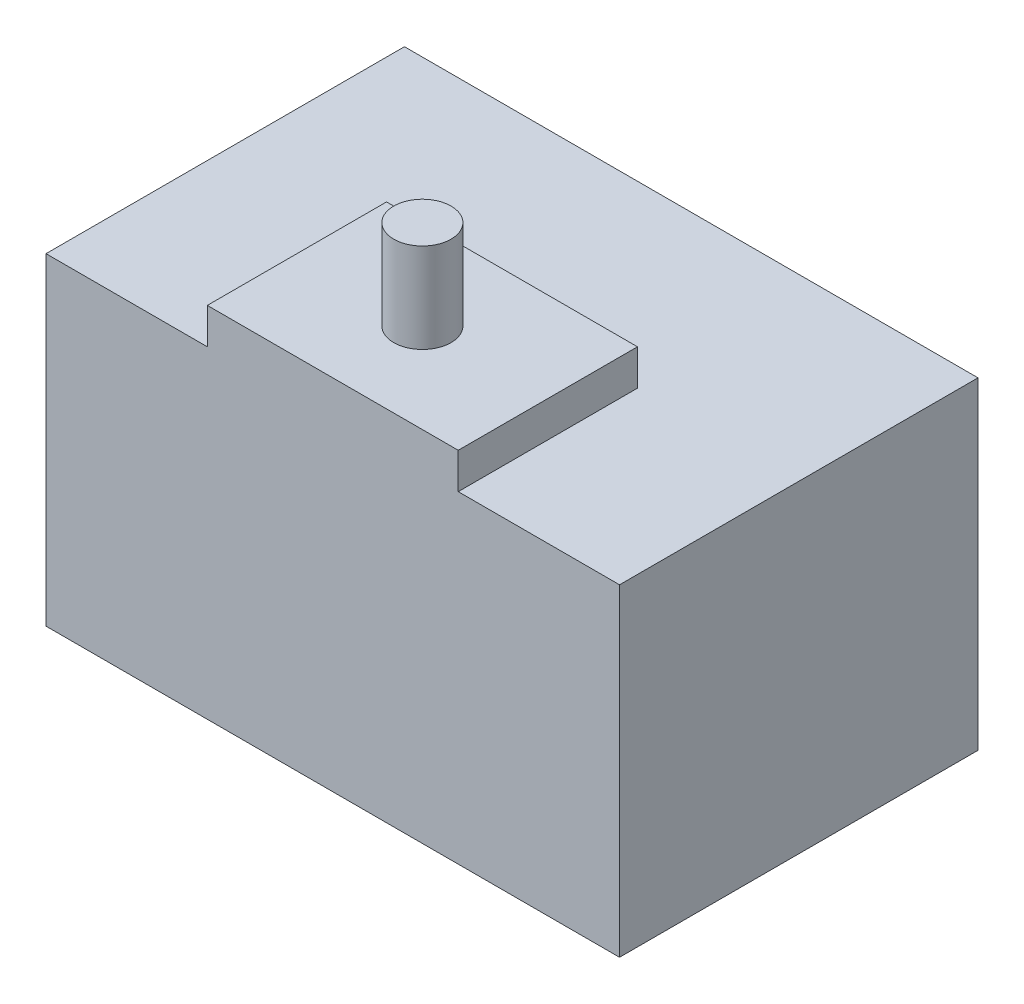
SolidWorks part; units mm, degrees
ref_plane "前视基准面" through (0, 0, 0) normal (0, 0, 1) x (1, 0, 0)
ref_plane "上视基准面" through (0, 0, 0) normal (0, 1, 0) x (1, 0, 0)
ref_plane "右视基准面" through (0, 0, 0) normal (1, 0, 0) x (0, 0, -1)
sketch "草图1" plane through (0, 0, 0) normal (0, 1, 0) x (1, 0, 0)
  line L1 (-800, 500) -> (800, 500)
  line L2 (-800, 500) -> (-800, -500)
  line L3 (-800, -500) -> (800, -500)
  line L4 (800, 500) -> (800, -500)
  line L5 (-800, 500) -> (800, -500) construction
  line L6 (-800, -500) -> (800, 500) construction
  point P0 (0, 0)
  dimension "D1" = 1600
  dimension "D2" = 1000
extrude "凸台-拉伸1" add sketch "草图1" along normal blind 900
sketch "草图2" plane through (0, 900, 0) normal (0, 1, 0) x (1, 0, 0)
  line L0 (-800, -500) -> (800, -500) construction
  line L1 (-350, 0) -> (350, 0)
  line L2 (-350, 0) -> (-350, -500)
  line L3 (-350, -500) -> (350, -500)
  line L4 (350, 0) -> (350, -500)
  line L5 (-350, 0) -> (350, -500) construction
  line L6 (-350, -500) -> (350, 0) construction
  point P0 (0, -250)
  dimension "D1" = 0
  dimension "D2" = 700
  dimension "D3" = 500
extrude "凸台-拉伸2" add sketch "草图2" along normal blind 100
sketch "草图3" plane through (0, 1000, 0) normal (0, 1, 0) x (1, 0, 0)
  line L0 (-350, 0) -> (-350, -500) construction
  line L1 (-300, -50) -> (300, -50) construction
  line L2 (-300, -50) -> (-300, -450) construction
  line L3 (-300, -450) -> (300, -450) construction
  line L4 (300, -50) -> (300, -450) construction
  line L5 (-300, -50) -> (300, -450) construction
  line L6 (-300, -450) -> (300, -50) construction
  line L7 (-350, -500) -> (350, -500) construction
  line L8 (350, -500) -> (350, 0) construction
  line L9 (350, 0) -> (-350, 0) construction
  circle A0 centre (-300, -50) radius 30
  circle A1 centre (300, -50) radius 30
  circle A2 centre (-300, -450) radius 30
  circle A3 centre (300, -450) radius 30
  point P0 (0, -250)
  dimension "D5" = 60
  dimension "D1" = 50
  dimension "D2" = 50
  dimension "D3" = 50
  dimension "D4" = 50
sketch "草图5" plane through (0, 1000, 0) normal (0, 1, 0) x (1, 0, 0)
  line L0 (350, 0) -> (-350, 0) construction
  circle A0 centre (0, -250) radius 80
  dimension "D3" = 160
  dimension "D1" = 0
  dimension "D2" = 250
extrude "凸台-拉伸5" add sketch "草图5" along normal blind 250
